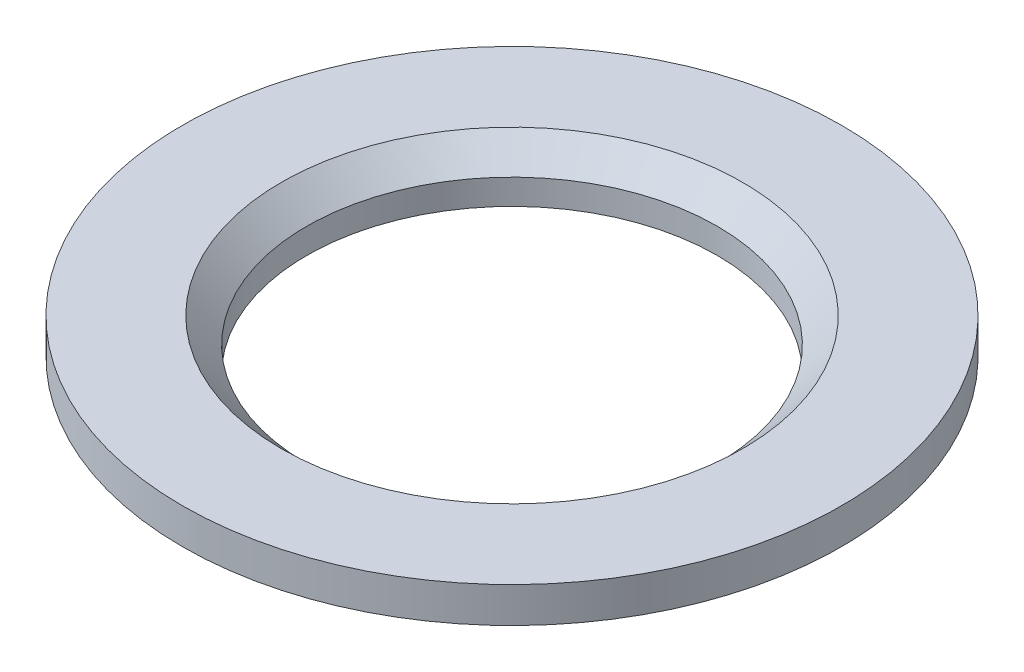
SolidWorks part; units mm, degrees
ref_plane "Front Plane" through (0, 0, 0) normal (0, 0, 1) x (1, 0, 0)
ref_plane "Top Plane" through (0, 0, 0) normal (0, 1, 0) x (1, 0, 0)
ref_plane "Right Plane" through (0, 0, 0) normal (1, 0, 0) x (0, 0, -1)
sketch "Sketch1" plane through (0, 0, 0) normal (0, 0, 1) x (1, 0, 0)
  line L0 (0, 2.7635) -> (0, -4.1478) construction
  line L1 (4.05, 0.5) -> (4.55, 1)
  line L2 (4.55, 1) -> (6.5, 1)
  line L3 (6.5, 1) -> (6.5, 0.3)
  line L4 (6.5, 0.3) -> (4.8, 0.3)
  line L5 (4.8, 0.3) -> (4.5, 0)
  line L6 (4.5, 0) -> (4.05, 0)
  line L7 (4.05, 0) -> (4.05, 0.5)
  dimension "D1" = 6.5
  dimension "D2" = 4.5
  dimension "D3" = 4.05
  dimension "D4" = 4.55
  dimension "D5" = 4.8
  dimension "D6" = 0.5
  dimension "D7" = 0.3
  dimension "D8" = 0.7
revolve "Revolve1" add sketch "Sketch1" angle 360 about L0
